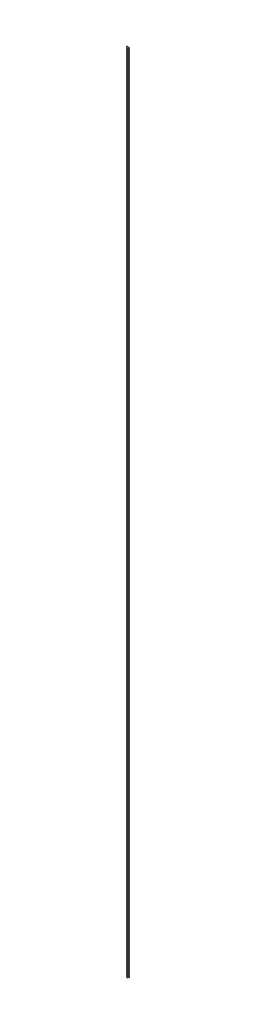
SolidWorks part; units mm, degrees
ref_plane "Front Plane" through (0, 0, 0) normal (0, 0, 1) x (1, 0, 0)
ref_plane "Top Plane" through (0, 0, 0) normal (0, 1, 0) x (1, 0, 0)
ref_plane "Right Plane" through (0, 0, 0) normal (1, 0, 0) x (0, 0, -1)
sketch "Sketch1" plane through (0, 0, 0) normal (0, 1, 0) x (1, 0, 0)
  line L1 (-31.75, -6.35) -> (31.75, -6.35)
  line L2 (31.75, -6.35) -> (31.75, -12.7)
  line L3 (31.75, -12.7) -> (12.7, -12.7)
  line L4 (12.7, -12.7) -> (12.7, -38.1)
  line L5 (12.7, -38.1) -> (-12.7, -38.1)
  line L6 (-12.7, -38.1) -> (-12.7, -12.7)
  line L7 (-12.7, -12.7) -> (-31.75, -12.7)
  line L8 (-31.75, -12.7) -> (-31.75, -6.35)
  point P4 (0, 0)
  point P13 (0, -6.35)
  dimension "D1" = 63.5
  dimension "D2" = 6.35
  dimension "D3" = 25.4
  dimension "D4" = 25.4
  dimension "D5" = 6.35
extrude "Boss-Extrude1" add sketch "Sketch1" along normal blind 18288 contours L6 L7 L8 L1 L2 L3 L4 L5
equation "\"Max_Rail_Width\"= 2.5"
equation "\"D1@Sketch1\"=\"Max_Rail_Width\""
equation "\"Rail_T_Thickness\"=0.25"
equation "\"D2@Sketch1\"=\"Rail_T_Thickness\""
equation "\"Rail_Support_Height\"=1"
equation "\"D3@Sketch1\"=\"Rail_Support_Height\""
equation "\"Rail_Support_Width\"=1"
equation "\"D4@Sketch1\"=\"Rail_Support_Width\""
equation "\"Gap\"=0.25"
equation "\"D5@Sketch1\"=\"Gap\""
equation "\"Length_of_Launch_Rail\"=720"
equation "\"D1@Boss-Extrude1\"=\"Length_of_Launch_Rail\""
